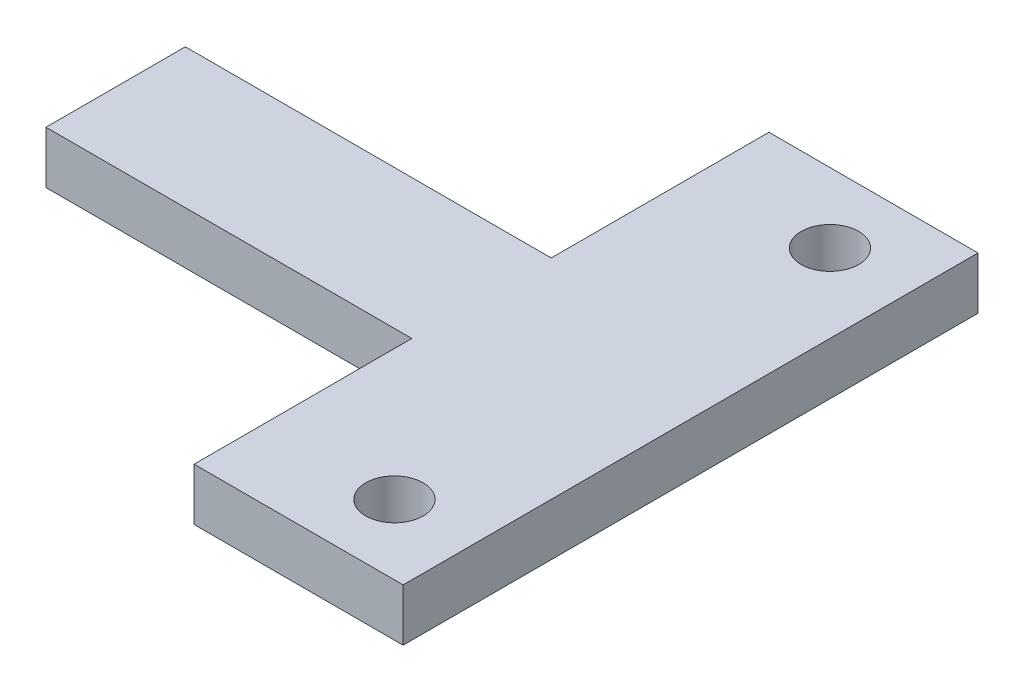
SolidWorks part; units mm, degrees
ref_plane "Front Plane" through (0, 0, 0) normal (0, 0, 1) x (1, 0, 0)
ref_plane "Top Plane" through (0, 0, 0) normal (0, 1, 0) x (1, 0, 0)
ref_plane "Right Plane" through (0, 0, 0) normal (1, 0, 0) x (0, 0, -1)
sketch "Sketch1" plane through (0, 0, 0) normal (0, 1, 0) x (1, 0, 0)
  line L0 (-10.5, 4) -> (-10.5, -4)
  line L1 (-10.5, -4) -> (10.5, -4)
  line L2 (10.5, -4) -> (10.5, -16.5)
  line L3 (10.5, -16.5) -> (22.5, -16.5)
  line L4 (22.5, -16.5) -> (22.5, 16.5)
  line L5 (22.5, 16.5) -> (10.5, 16.5)
  line L6 (10.5, 16.5) -> (10.5, 4)
  line L7 (10.5, 4) -> (-10.5, 4)
  line L8 (18, 12.5) -> (18, -12.5) construction
  circle A0 centre (18, 12.5) radius 1.65
  circle A1 centre (18, -12.5) radius 1.65
  point P9 (22.5, 0)
  point P14 (18, 0)
  point P16 (0, 4)
  dimension "D3" = 3.3
  dimension "D1" = 8
  dimension "D2" = 21
  dimension "D4" = 12
  dimension "D5" = 33
  dimension "D6" = 25
  dimension "D7" = 4.5
extrude "Boss-Extrude1" add sketch "Sketch1" along normal blind 3
